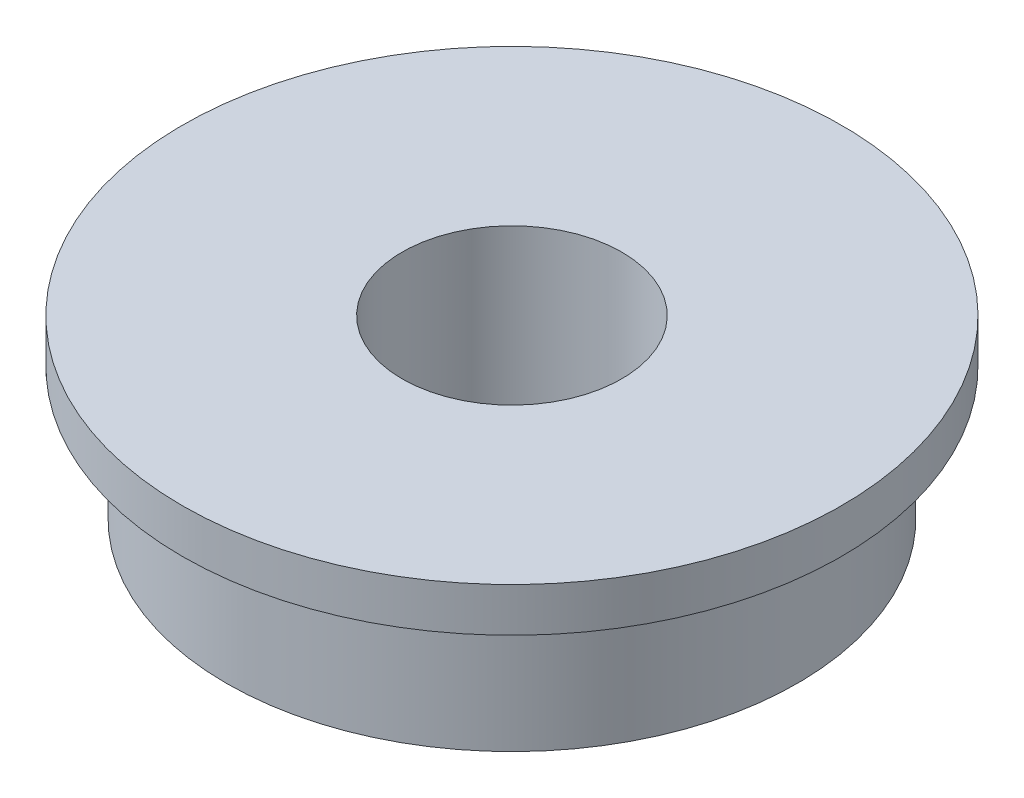
SolidWorks part; units mm, degrees
ref_plane "Front Plane" through (0, 0, 0) normal (0, 0, 1) x (1, 0, 0)
ref_plane "Top Plane" through (0, 0, 0) normal (0, 1, 0) x (1, 0, 0)
ref_plane "Right Plane" through (0, 0, 0) normal (1, 0, 0) x (0, 0, -1)
other "Bounding Box"
ref_plane "Default Plane" through (-8.9266, -12.7485, 0) normal (-0.1736, 0.9848, 0) x (0.9848, 0.1736, 0)
sketch "Sketch1" plane through (0, 0, 0) normal (0, 1, 0) x (1, 0, 0)
  circle A0 centre (0, 0) radius 2.5
  circle A1 centre (0, 0) radius 6.5
  dimension "D1" = 5
  dimension "D2" = 13
extrude "Boss-Extrude1" add sketch "Sketch1" along normal mid plane 4
sketch "Sketch2" plane through (0, 2, 0) normal (0, 1, 0) x (1, 0, 0)
  circle A0 centre (0, 0) radius 7.5
  circle A1 centre (0, 0) radius 6.5
  circle A2 centre (0, 0) radius 6.5
  dimension "D2" = 15
  dimension "D1" = 0
extrude "Boss-Extrude2" add sketch "Sketch2" against normal blind 1
